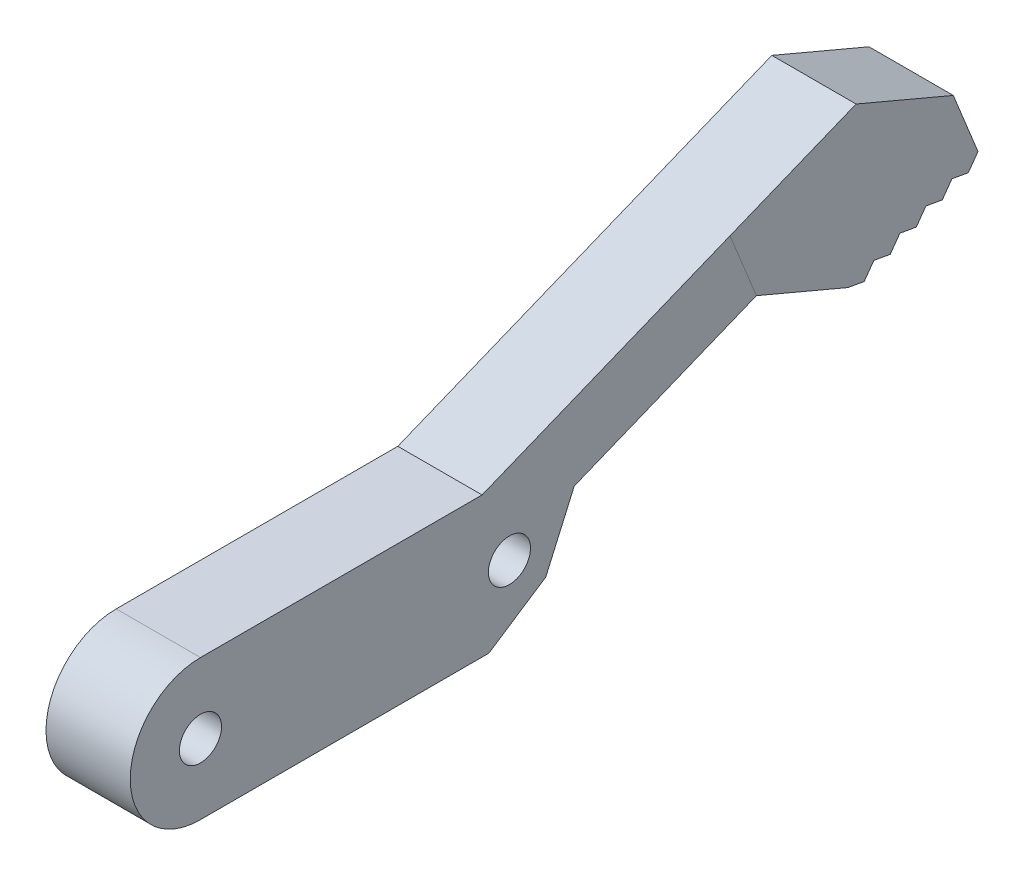
SolidWorks part; units mm, degrees
material "PLA"
ref_plane "Front Plane" through (0, 0, 0) normal (0, 0, 1) x (1, 0, 0)
ref_plane "Top Plane" through (0, 0, 0) normal (0, 1, 0) x (1, 0, 0)
ref_plane "Right Plane" through (0, 0, 0) normal (1, 0, 0) x (0, 0, -1)
sketch "Sketch1" plane through (0, 0, 0) normal (1, 0, 0) x (0, 0, -1)
  line L1 (0, 0) -> (27, 0)
  line L2 (0, 0) -> (0, 10)
  line L3 (0, 10) -> (27, 10)
  circle A0 centre (5, 5) radius 1.5
  circle A1 centre (5, 5) radius 5
  circle A2 centre (27, 5) radius 5
  circle A3 centre (27, 5) radius 1.5
  dimension "D7" = 3
  dimension "D11" = 10
  dimension "D2" = 3
  dimension "D1" = 10
  dimension "D8" = 5
  dimension "D9" = 5
  dimension "D10" = 22
extrude "Boss-Extrude1" add sketch "Sketch1" along normal blind 6 contours A1 A0 | A2 L3 A1 L1 | A2 A3
sketch "Sketch2" plane through (6, 0, 0) normal (1, 0, 0) x (0, 0, -1)
  line L0 (27, 0) -> (60.3654, 13.5185)
  line L1 (5, 0) -> (27, 0) construction
  line L3 (60.3654, 13.5185) -> (56.6103, 22.7866)
  line L5 (56.6103, 22.7866) -> (25.0511, 10)
  line L6 (5, 10) -> (27, 10) construction
  line L7 (31.6102, 7.2627) -> (44.5856, 12.5199)
  line L8 (31.6102, 7.2627) -> (28.8536, 0.751)
  line L9 (44.5856, 12.5199) -> (51.0972, 9.7633)
  line L10 (51.0972, 9.7633) -> (60.3654, 13.5185)
  line L11 (51.0972, 9.7633) -> (51.3338, 9.1794)
  line L12 (60.3654, 13.5185) -> (60.602, 12.9346)
  line L13 (51.3338, 9.1794) -> (60.602, 12.9346)
  line L14 (5, 10) -> (27, 10)
  arc A3 (27, 0) -> (27, 10) centre (27, 5) ccw construction
  arc A4 (27, 0) -> (27, 10) centre (27, 5) ccw
  line M1 (27, 10) -> (5, 10)
  arc M4 (27, 0) -> (27, 10) centre (27, 5) ccw
  dimension "D1" = 157.944
  dimension "D2" = 36
  dimension "D3" = 90
  dimension "D4" = 10
  dimension "D5" = 10
  dimension "D6" = 45
  dimension "D7" = 45
  dimension "D8" = 5
  dimension "D9" = 5
  dimension "D10" = 14
  dimension "D11" = 0.63
extrude "Boss-Extrude2" add sketch "Sketch2" against normal blind 6 contours L7 L9 L0 L3 L5 L8 M1 M4 | L11 L13 L12 L0
sketch "Sketch4" plane through (6, 0, 0) normal (1, 0, 0) x (0, 0, -1)
  line L0 (51.6843, 20.7908) -> (58.6061, 17.8606)
  line L1 (56.6103, 22.7866) -> (25.0511, 10) construction
  line L2 (60.602, 12.9346) -> (56.6103, 22.7866) construction
  line L3 (44.5856, 12.5199) -> (51.0972, 9.7633) construction
  line L4 (56.6103, 22.7866) -> (25.0511, 10)
  line L5 (60.602, 12.9346) -> (56.6103, 22.7866)
  line M8 (60.602, 12.9346) -> (56.6103, 22.7866)
  line M9 (56.6103, 22.7866) -> (25.0511, 10)
extrude "Cut-Extrude2" cut sketch "Sketch4" against normal through all contours L0 M9 M8
sketch "Sketch5" plane through (6, 0, 0) normal (1, 0, 0) x (0, 0, -1)
  line L0 (31.5395, 7.0959) -> (29.5838, 2.665)
  line L1 (29.5838, 2.665) -> (25.5396, 0)
  line L2 (5, 0) -> (27, 0) construction
  line L3 (51.0972, 9.7633) -> (60.3654, 13.5185) construction
  line L4 (60.602, 12.9346) -> (58.6061, 17.8606) construction
  line L5 (51.0972, 9.7633) -> (52.2606, 9.5549)
  line L6 (51.3338, 9.1794) -> (60.602, 12.9346) construction
  line L7 (52.2606, 9.5549) -> (52.9509, 10.5144)
  line L8 (52.9509, 10.5144) -> (54.1143, 10.306)
  line L9 (54.1143, 10.306) -> (54.8045, 11.2654)
  line L10 (54.8045, 11.2654) -> (55.9679, 11.057)
  line L11 (55.9679, 11.057) -> (56.6582, 12.0164)
  line L12 (56.6582, 12.0164) -> (57.8215, 11.808)
  line L13 (57.8215, 11.808) -> (58.5118, 12.7674)
  line L14 (58.5118, 12.7674) -> (59.6752, 12.559)
  line L15 (59.6752, 12.559) -> (60.3654, 13.5185)
  line L16 (51.0972, 9.7633) -> (51.3338, 9.1794) construction
  line L17 (51.3338, 9.1794) -> (60.602, 12.9346)
  line L18 (51.0972, 9.7633) -> (51.3338, 9.1794)
  line L19 (60.602, 12.9346) -> (60.3654, 13.5185)
  line L20 (25.5396, 0) -> (27, 0)
  arc A0 (27, 0) -> (31.5395, 7.0959) centre (27, 5) ccw construction
  arc A1 (27, 0) -> (31.5395, 7.0959) centre (27, 5) ccw
  line M7 (5, 0) -> (27, 0)
  arc M8 (27, 0) -> (31.5395, 7.0959) centre (27, 5) ccw
  line M12 (51.0972, 9.7633) -> (51.3338, 9.1794)
  line M13 (51.3338, 9.1794) -> (60.602, 12.9346)
  line M14 (60.602, 12.9346) -> (58.6061, 17.8606)
  dimension "D1" = 4.8433
  dimension "D2" = 147.2
  dimension "D3" = 2
  dimension "D4" = 5
extrude "Cut-Extrude3" cut sketch "Sketch5" against normal blind 10 contours L0 L1 M7 M8 | L5 M12 M13 | L8 L7 M13 | L10 L9 M13 | L12 L11 M13 | L14 L13 M13 | L15 M13 M14
sketch "Esboço1" plane through (6, 0, 0) normal (1, 0, 0) x (0, 0, -1)
  line L0 (44.5856, 12.5199) -> (42.708, 17.1539)
  line L1 (51.6843, 20.7908) -> (25.0511, 10) construction
  line L22 (58.5118, 12.7674) -> (59.6752, 12.559)
  line L23 (59.6752, 12.559) -> (60.3654, 13.5185)
  line L24 (60.3654, 13.5185) -> (58.6061, 17.8606)
  line L25 (58.6061, 17.8606) -> (51.6843, 20.7908)
  line L26 (51.6843, 20.7908) -> (25.0511, 10)
  line L27 (25.0511, 10) -> (5, 10)
  line L28 (5, 0) -> (25.5396, 0)
  line L29 (25.5396, 0) -> (29.5838, 2.665)
  line L30 (29.5838, 2.665) -> (31.5395, 7.0959)
  line L31 (31.5395, 7.0959) -> (31.6102, 7.2627)
  line L32 (31.6102, 7.2627) -> (44.5856, 12.5199)
  line L33 (44.5856, 12.5199) -> (51.0972, 9.7633)
  line L34 (51.0972, 9.7633) -> (52.2606, 9.5549)
  line L35 (52.2606, 9.5549) -> (52.9509, 10.5144)
  line L36 (52.9509, 10.5144) -> (54.1143, 10.306)
  line L37 (54.1143, 10.306) -> (54.8045, 11.2654)
  line L38 (54.8045, 11.2654) -> (55.9679, 11.057)
  line L39 (55.9679, 11.057) -> (56.6582, 12.0164)
  line L40 (56.6582, 12.0164) -> (57.8215, 11.808)
  line L41 (57.8215, 11.808) -> (58.5118, 12.7674)
  line L42 (58.5118, 12.7674) -> (59.6752, 12.559)
  line L43 (59.6752, 12.559) -> (60.3654, 13.5185)
  line L44 (60.3654, 13.5185) -> (58.6061, 17.8606)
  line L45 (58.6061, 17.8606) -> (51.6843, 20.7908)
  line L46 (51.6843, 20.7908) -> (42.708, 17.1539)
  line L53 (44.5856, 12.5199) -> (51.0972, 9.7633)
  line L54 (51.0972, 9.7633) -> (52.2606, 9.5549)
  line L55 (52.2606, 9.5549) -> (52.9509, 10.5144)
  line L56 (52.9509, 10.5144) -> (54.1143, 10.306)
  line L57 (54.1143, 10.306) -> (54.8045, 11.2654)
  line L58 (54.8045, 11.2654) -> (55.9679, 11.057)
  line L59 (55.9679, 11.057) -> (56.6582, 12.0164)
  line L60 (56.6582, 12.0164) -> (57.8215, 11.808)
  line L61 (57.8215, 11.808) -> (58.5118, 12.7674)
  arc A1 (5, 10) -> (5, 0) centre (5, 5) ccw
  point P5 (42.983, 17.2654)
  dimension "D1" = 0
split line "Linha de divisão1"
